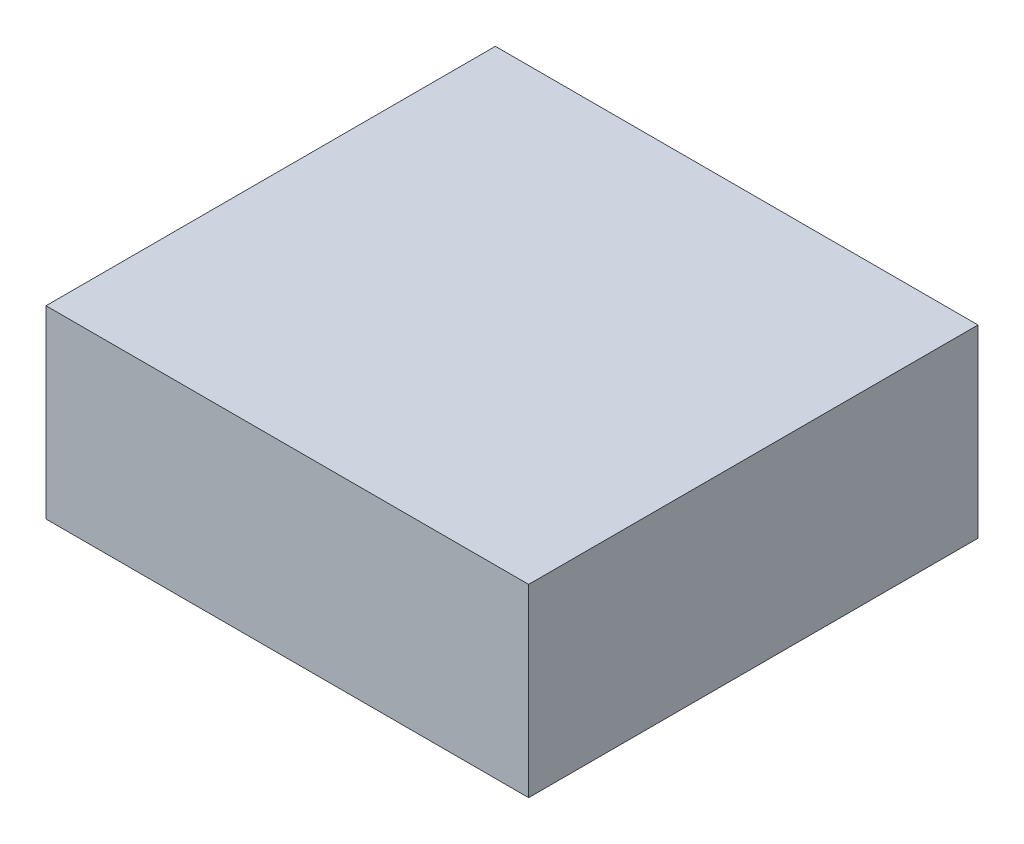
SolidWorks part; units mm, degrees
ref_plane "Front Plane" through (0, 0, 0) normal (0, 0, 1) x (1, 0, 0)
ref_plane "Top Plane" through (0, 0, 0) normal (0, 1, 0) x (1, 0, 0)
ref_plane "Right Plane" through (0, 0, 0) normal (1, 0, 0) x (0, 0, -1)
sketch "Sketch1" plane through (0, 0, 0) normal (0, 1, 0) x (1, 0, 0)
  line L1 (-53.7742, 13.7987) -> (19.8858, 13.7987)
  line L2 (-53.7742, 13.7987) -> (-53.7742, -54.7813)
  line L3 (-53.7742, -54.7813) -> (19.8858, -54.7813)
  line L4 (19.8858, 13.7987) -> (19.8858, -54.7813)
  dimension "D1" = 68.58
  dimension "D2" = 73.66
extrude "Boss-Extrude1" add sketch "Sketch1" along normal blind 28.194
sketch "Sketch2" plane through (0, 0, 0) normal (0, -1, 0) x (1, 0, 0)
  line L0 (-53.7742, -13.7987) -> (-53.7742, 54.7813) construction
  line L1 (-47.4242, 48.4313) -> (13.5358, 48.4313)
  line L2 (-47.4242, 48.4313) -> (-47.4242, -7.4487)
  line L3 (-47.4242, -7.4487) -> (13.5358, -7.4487)
  line L4 (13.5358, 48.4313) -> (13.5358, -7.4487)
  line L5 (19.8858, -13.7987) -> (-53.7742, -13.7987) construction
  line L6 (-53.7742, 54.7813) -> (19.8858, 54.7813) construction
  line L7 (19.8858, 54.7813) -> (19.8858, -13.7987) construction
  dimension "D1" = 6.35
  dimension "D2" = 6.35
  dimension "D3" = 6.35
  dimension "D4" = 6.35
extrude "Cut-Extrude1" cut sketch "Sketch2" against normal blind 21.844
